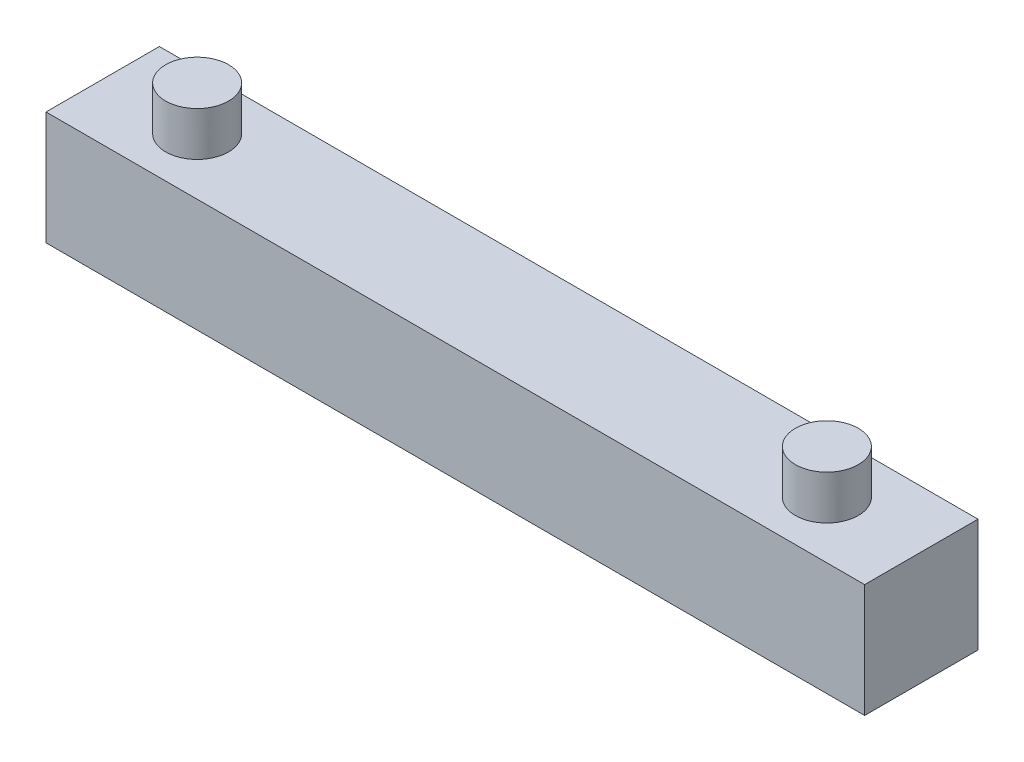
SolidWorks part; units mm, degrees
ref_plane "Front Plane" through (0, 0, 0) normal (0, 0, 1) x (1, 0, 0)
ref_plane "Top Plane" through (0, 0, 0) normal (0, 1, 0) x (1, 0, 0)
ref_plane "Right Plane" through (0, 0, 0) normal (1, 0, 0) x (0, 0, -1)
sketch "Sketch1" plane through (0, 0, 0) normal (0, 1, 0) x (1, 0, 0)
  line L1 (0, 0) -> (65, 0)
  line L2 (0, 0) -> (0, 9)
  line L3 (0, 9) -> (65, 9)
  line L4 (65, 0) -> (65, 9)
  dimension "D1" = 65
  dimension "D2" = 9
extrude "Boss-Extrude1" add sketch "Sketch1" along normal blind 9
sketch "Sketch2" plane through (0, 9, 0) normal (0, 1, 0) x (1, 0, 0)
  line L0 (0, 9) -> (0, 0) construction
  line L1 (0, 0) -> (65, 0) construction
  circle A0 centre (7.5, 4.5) radius 2.5
  circle A1 centre (57.5, 4.5) radius 2.5
  dimension "D1" = 5
  dimension "D2" = 4.5
  dimension "D3" = 50
  dimension "D4" = 7.5
extrude "Boss-Extrude2" add sketch "Sketch2" along normal blind 3.5
